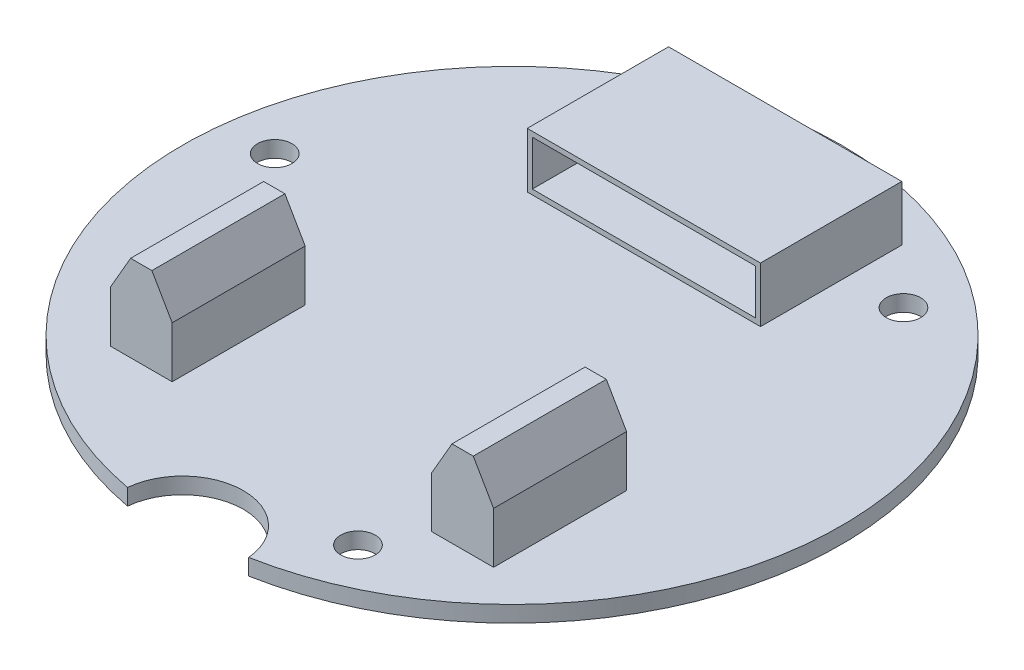
SolidWorks part; units mm, degrees
ref_plane "Front Plane" through (0, 0, 0) normal (0, 0, 1) x (1, 0, 0)
ref_plane "Top Plane" through (0, 0, 0) normal (0, 1, 0) x (1, 0, 0)
ref_plane "Right Plane" through (0, 0, 0) normal (1, 0, 0) x (0, 0, -1)
sketch "Sketch2" plane through (0, 0, 0) normal (0, 1, 0) x (1, 0, 0)
  line L0 (0, 0) -> (17.859, -44.2025) construction
  line L1 (0, 0) -> (0, -32.5) construction
  arc A0 (5.9744, -31.9462) -> (-5.9744, -31.9462) centre (0, 0) ccw
  circle A1 centre (0, 0) radius 27.5 construction
  arc A2 (5.9744, -31.9462) -> (-5.9744, -31.9462) centre (0, -32.5) ccw
  circle A3 centre (10.3017, -25.4976) radius 1.7 construction
  dimension "D1" = 65
  dimension "D2" = 55
  dimension "D3" = 12
  dimension "D5" = 3.4
  dimension "D4" = 22
extrude "Boss-Extrude2" add sketch "Sketch2" along normal blind 1.6 contours A0 A2
sketch "Sketch3" plane through (0, 1.6, 0) normal (0, 1, 0) x (1, 0, 0)
  circle A0 centre (10.3017, -25.4976) radius 1.7 construction
  circle A1 centre (10.3017, -25.4976) radius 1.7
extrude "Cut-Extrude1" cut sketch "Sketch3" against normal through all
pattern_circular "CirPattern1" count 3 over 360 about axis through (0, 0, 0) along (0, 1, 0) of "Cut-Extrude1"
sketch "Sketch4" plane through (0, 0, 0) normal (1, 0, 0) x (0, 0, -1)
  line L0 (32.5, 1.6) -> (-31.9462, 1.6) construction
  line L1 (13, 1.6) -> (26.9343, 1.6)
  line L2 (13, 1.6) -> (13, 7.0356)
  line L3 (13, 7.0356) -> (26.9343, 7.0356)
  line L4 (26.9343, 1.6) -> (26.9343, 7.0356)
  dimension "D1" = 13
  dimension "D2" = 5.4356
  dimension "D3" = 13.9343
extrude "Boss-Extrude3" add sketch "Sketch4" along normal mid plane 23
ref_plane "Plane1" through (0, 0, 7.6) normal (0, 0, 1) x (1, 0, 0)
sketch "Sketch5" plane through (0, 0, 7.6) normal (0, 0, 1) x (1, 0, 0)
  line L0 (32.5, 1.6) -> (-32.5, 1.6) construction
  line L1 (12.8, 1.6) -> (18.896, 1.6)
  line L2 (12.8, 1.6) -> (12.8, 10.1)
  line L3 (12.8, 10.1) -> (18.896, 10.1)
  line L4 (18.896, 1.6) -> (18.896, 10.1)
  line L5 (0, -42.1864) -> (0, 42.1864) construction
  dimension "D1" = 12.8
  dimension "D2" = 8.5
  dimension "D3" = 6.096
extrude "Boss-Extrude4" add sketch "Sketch5" along normal blind 13.1191
chamfer "Chamfer1" distance 2 angle 60 2 edges at (18.896, 10.1, 14.1595) (12.8, 10.1, 14.1595)
mirror "Mirror1" about plane through (0, 0, 0) normal (1, 0, 0) of "Boss-Extrude4", "Chamfer1"
sketch "Sketch6" plane through (0, 0, -13) normal (0, 0, 1) x (1, 0, 0)
  line L8 (-11, 6.5356) -> (-11, 2.1)
  line L9 (-11, 2.1) -> (11, 2.1)
  line L10 (11, 2.1) -> (11, 6.5356)
  line L11 (11, 6.5356) -> (-11, 6.5356)
  line L12 (-11, 6.5356) -> (-11, 2.1)
  line L13 (-11, 2.1) -> (11, 2.1)
  line L14 (11, 2.1) -> (11, 6.5356)
  line L15 (11, 6.5356) -> (-11, 6.5356)
  dimension "D1" = 0.5
extrude "Cut-Extrude2" cut sketch "Sketch6" against normal offset from surface (13.4343 mm away) 0.5 up to face at (0, 4.3178, -26.9343)
sketch "Sketch8" plane through (0, 0, 0) normal (0, -1, 0) x (1, 0, 0)
  line L0 (12.8, 20.7191) -> (12.8, 7.6) construction
  line L1 (12.8, 20.7191) -> (18.896, 20.7191) construction
  line L2 (18.896, 20.7191) -> (18.896, 7.6) construction
  line L3 (12.8, 7.6) -> (18.896, 7.6) construction
  line L4 (-12.8, 7.6) -> (-18.896, 7.6) construction
  line L5 (-12.8, 20.7191) -> (-12.8, 7.6) construction
  line L6 (-12.8, 20.7191) -> (-18.896, 20.7191) construction
  line L7 (-18.896, 20.7191) -> (-18.896, 7.6) construction
  line L8 (12.8, 20.7191) -> (12.8, 7.6)
  line L9 (12.8, 20.7191) -> (18.896, 20.7191)
  line L10 (18.896, 20.7191) -> (18.896, 7.6)
  line L11 (12.8, 7.6) -> (18.896, 7.6)
  line L12 (-12.8, 7.6) -> (-18.896, 7.6)
  line L13 (-12.8, 20.7191) -> (-12.8, 7.6)
  line L14 (-12.8, 20.7191) -> (-18.896, 20.7191)
  line L15 (-18.896, 20.7191) -> (-18.896, 7.6)
extrude "Boss-Extrude5" add sketch "Sketch8" along normal blind 2
sketch "Sketch9" [suppressed] plane through (0, 1.6, 0) normal (0, 1, 0) x (1, 0, 0)
  line L0 (32.5, 1.324) -> (32.5, -13.9025) construction
  line L1 (27.6994, 5.084) -> (30.9506, 5.084)
  line L2 (27.6994, 5.084) -> (27.6994, -6.6)
  line L3 (27.6994, -6.6) -> (30.9506, -6.6)
  line L4 (30.9506, 5.084) -> (30.9506, -6.6)
  line L5 (-6.655, -7.6) -> (6.655, -7.6) construction
  arc A0 (5.9744, -31.9462) -> (-5.9744, -31.9462) centre (0, 0) ccw construction
  dimension "D1" = 11.684
  dimension "D2" = 3.2512
  dimension "D3" = 3.0988
  dimension "D4" = 1
extrude "Extrude-Thin1" [suppressed] add sketch "Sketch9" along normal blind 4.064 thin
